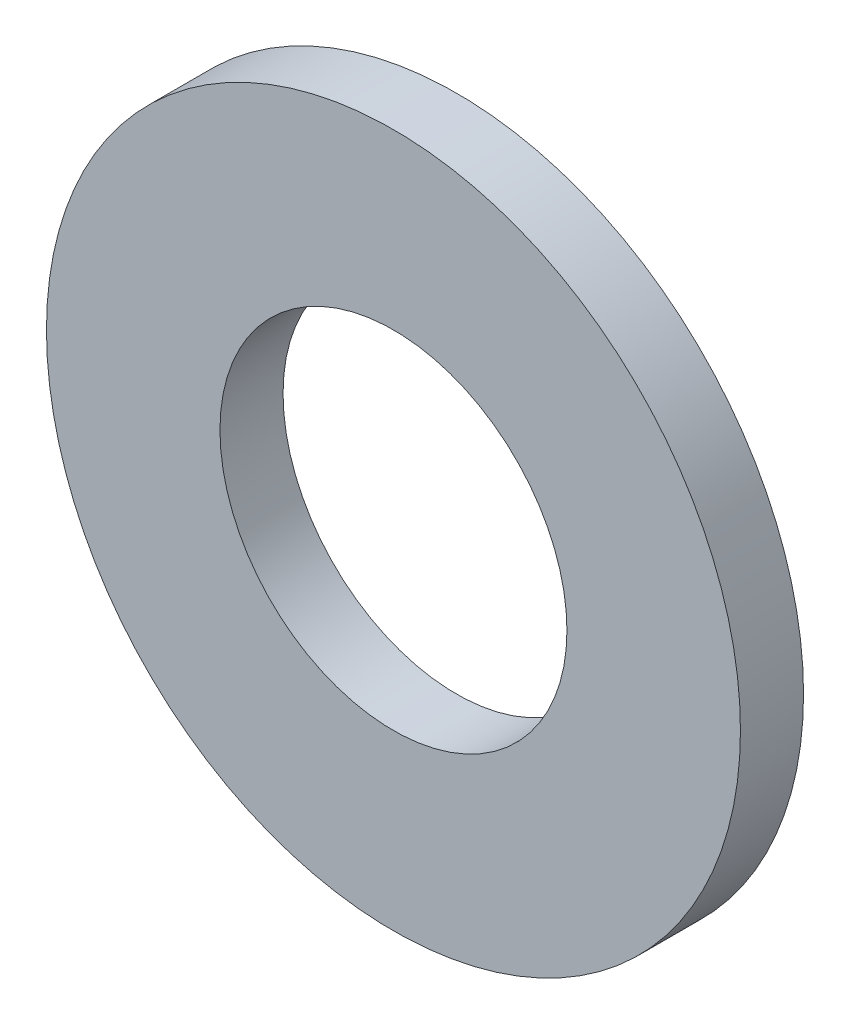
SolidWorks part; units mm, degrees
material "Сталь"
ref_plane "Спереди" through (0, 0, 0) normal (0, 0, 1) x (1, 0, 0)
ref_plane "Сверху" through (0, 0, 0) normal (0, 1, 0) x (1, 0, 0)
ref_plane "Справа" through (0, 0, 0) normal (1, 0, 0) x (0, 0, -1)
sketch "Эскиз1" plane through (0, 0, 0) normal (0, 0, 1) x (1, 0, 0)
  circle A0 centre (0, 0) radius 2.75
  circle A1 centre (0, 0) radius 5.5
  dimension "D1" = 5.5
  dimension "D2" = 11
extrude "Бобышка-Вытянуть1" add sketch "Эскиз1" along normal blind 1
